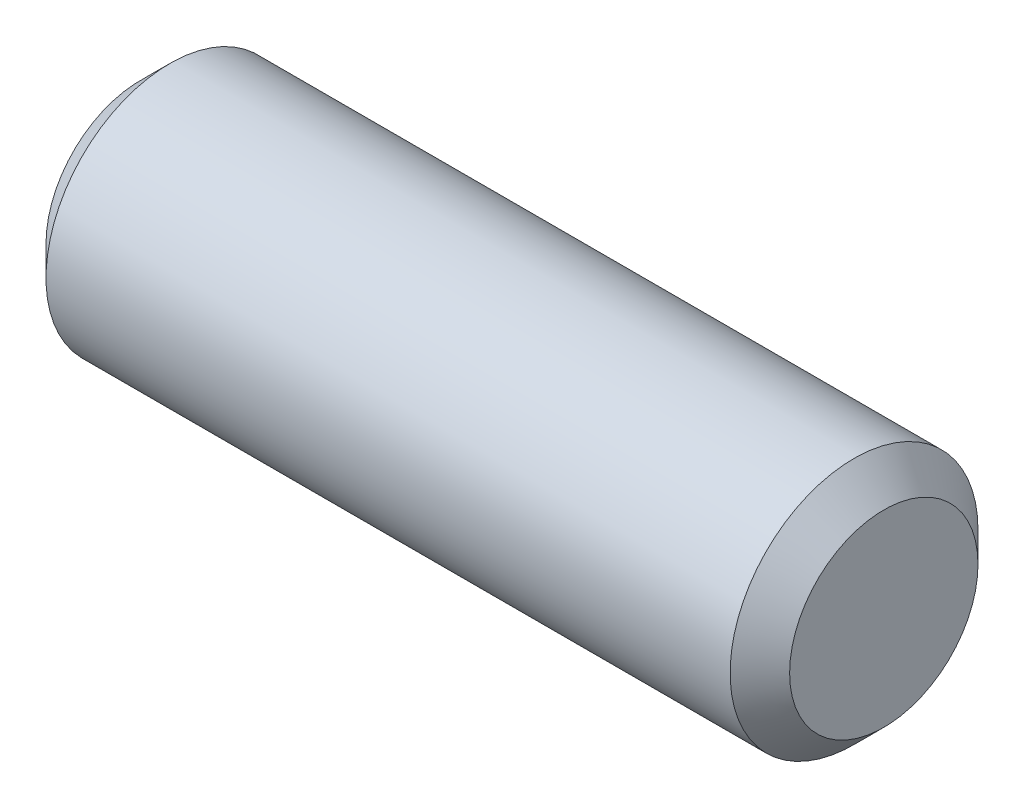
SolidWorks part; units mm, degrees
material "ABS"
ref_plane "Front Plane" through (0, 0, 0) normal (0, 0, 1) x (1, 0, 0)
ref_plane "Top Plane" through (0, 0, 0) normal (0, 1, 0) x (1, 0, 0)
ref_plane "Right Plane" through (0, 0, 0) normal (1, 0, 0) x (0, 0, -1)
sketch "Sketch2" plane through (0, 0, 0) normal (1, 0, 0) x (0, 0, -1)
  circle A0 centre (0, 0) radius 6.35
  dimension "D1" = 12.7
extrude "Boss-Extrude1" add sketch "Sketch2" along normal blind 38.1
chamfer "Chamfer1" distance 1.524 angle 45 1 edges at (38.1, 0, -6.35)
chamfer "Chamfer2" distance 1.524 angle 45 1 edges at (0, 0, -6.35)
